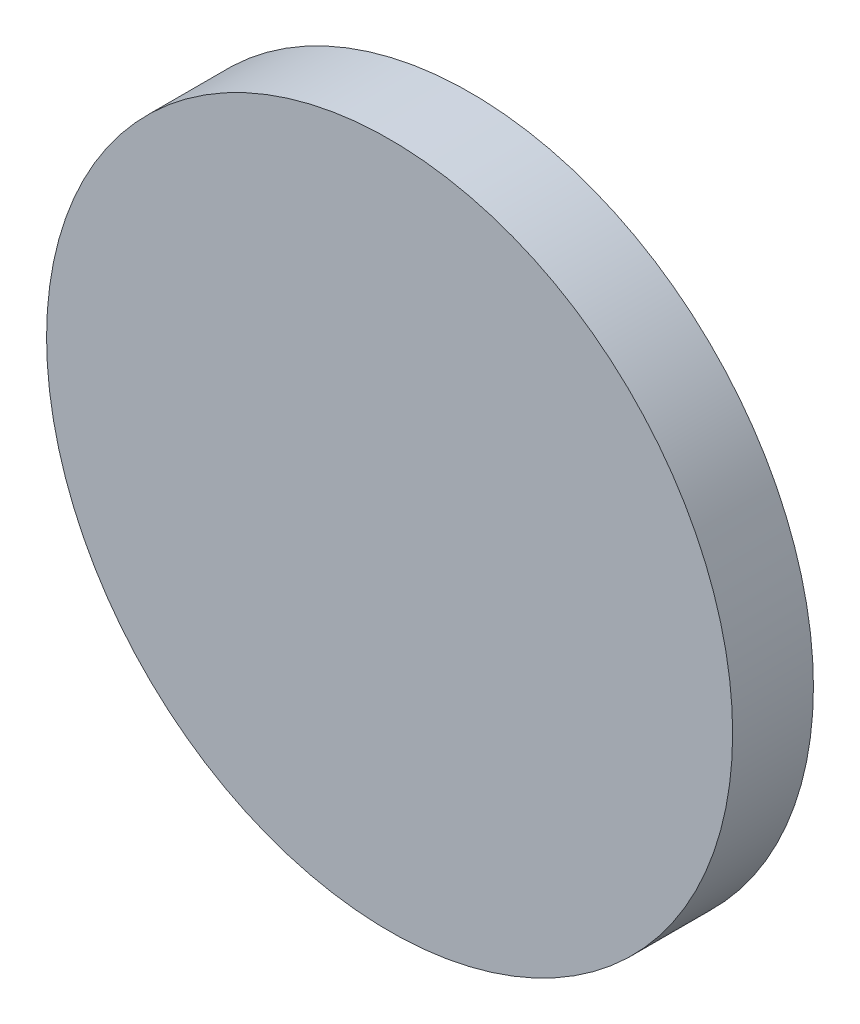
SolidWorks part; units mm, degrees
ref_plane "Front Plane" through (0, 0, 0) normal (0, 0, 1) x (1, 0, 0)
ref_plane "Top Plane" through (0, 0, 0) normal (0, 1, 0) x (1, 0, 0)
ref_plane "Right Plane" through (0, 0, 0) normal (1, 0, 0) x (0, 0, -1)
sketch "Sketch1" plane through (0, 0, 0) normal (0, 0, 1) x (1, 0, 0)
  circle A0 centre (0, 0) radius 25.48
  dimension "D1" = 50.96
extrude "Boss-Extrude1" add sketch "Sketch1" along normal blind 6
ref_plane "Plane1" through (0, 0, -3) normal (0, 0, 1) x (1, 0, 0)
sketch "Sketch10" plane through (0, 0, 0) normal (0, 0, -1) x (-1, 0, 0)
  circle A0 centre (0, 13.4214) radius 2
  circle A1 centre (11.6233, 6.7107) radius 2
  circle A2 centre (11.6233, -6.7107) radius 2
  circle A3 centre (0, -13.4214) radius 2
  circle A4 centre (-11.6233, -6.7107) radius 2
  circle A5 centre (-11.6233, 6.7107) radius 2
  dimension "D1" = 4
  dimension "D2" = 6
extrude "Boss-Extrude3" add sketch "Sketch10" along normal blind 2
